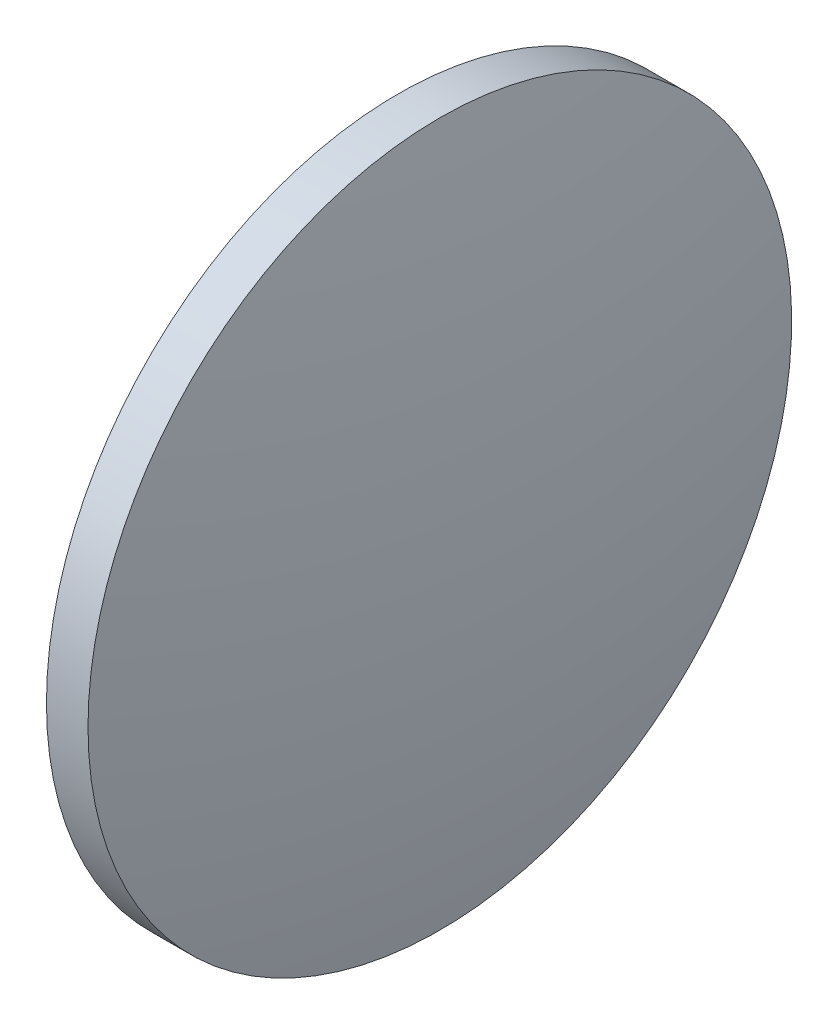
SolidWorks part; units mm, degrees
ref_plane "前视基准面" through (0, 0, 0) normal (0, 0, 1) x (1, 0, 0)
ref_plane "上视基准面" through (0, 0, 0) normal (0, 1, 0) x (1, 0, 0)
ref_plane "右视基准面" through (0, 0, 0) normal (1, 0, 0) x (0, 0, -1)
sketch "草图1" plane through (0, 0, 0) normal (0, 0, 1) x (1, 0, 0)
  line L0 (220.3307, 130.4671) -> (257.9227, 130.4671) construction
  line L1 (232.0208, 130.4671) -> (232.0208, 155.8671)
  line L2 (232.0208, 155.8671) -> (235.0208, 155.8671)
  line L3 (237.4208, 130.4671) -> (232.0208, 130.4671)
  arc A0 (237.4208, 130.4671) -> (235.0208, 155.8671) centre (101.8125, 130.4671) ccw
revolve "旋转1" add sketch "草图1" angle 360 about L0
